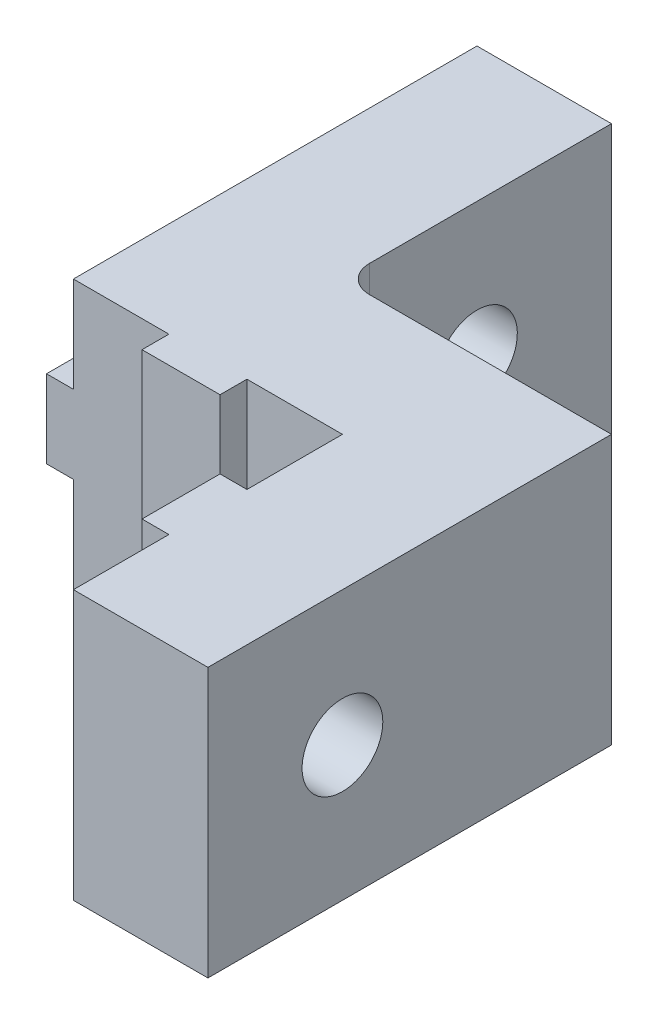
SolidWorks part; units mm, degrees
ref_plane "Front Plane" through (0, 0, 0) normal (0, 0, 1) x (1, 0, 0)
ref_plane "Top Plane" through (0, 0, 0) normal (0, 1, 0) x (1, 0, 0)
ref_plane "Right Plane" through (0, 0, 0) normal (1, 0, 0) x (0, 0, -1)
sketch "Sketch1" plane through (0, 0, 0) normal (0, 0, 1) x (1, 0, 0)
  line L0 (0, 10) -> (0, 6.45)
  line L1 (0, 6.45) -> (-1, 6.45)
  line L2 (-1, 6.45) -> (-1, 3.55)
  line L3 (-1, 3.55) -> (0, 3.55)
  line L4 (0, 3.55) -> (0, 0)
  line L5 (0, 0) -> (15, 0)
  line L6 (15, 0) -> (15, 10)
  line L7 (15, 10) -> (0, 10)
  dimension "D1" = 1
  dimension "D2" = 10
  dimension "D3" = 2.9
  dimension "D4" = 15
extrude "Main" add sketch "Sketch1" along normal blind 25
sketch "Sketch2" plane through (0, 0, 0) normal (0, -1, 0) x (-1, 0, 0)
  line L0 (0, -25) -> (0, 0) construction
  line L1 (1, -15) -> (1, -25)
  line L2 (-15, 0) -> (-5, 0)
  line L3 (1, -25) -> (-10, -25)
  line L4 (-15, 0) -> (-15, -10)
  line L5 (-15, -10) -> (-5, -10)
  line L6 (1, -25) -> (1, 0) construction
  line L7 (-5, 0) -> (-5, -10)
  line L8 (-10, -25) -> (-10, -21.45)
  line L9 (0, -25) -> (0, 0) construction
  line L10 (0, -25) -> (-15, -25) construction
  line L11 (-10, -21.45) -> (-9, -21.45)
  line L12 (-9, -21.45) -> (-9, -18.55)
  line L13 (-9, -18.55) -> (-10, -18.55)
  line L14 (-10, -18.55) -> (-10, -15)
  line L15 (-10, -15) -> (-6.45, -15)
  line L16 (-6.45, -15) -> (-6.45, -16)
  line L17 (-6.45, -16) -> (-3.55, -16)
  line L18 (-3.55, -16) -> (-3.55, -15)
  line L19 (-3.55, -15) -> (1, -15)
  dimension "D1" = 10
  dimension "D2" = 5
  dimension "D3" = 10
  dimension "D4" = 1
  dimension "D5" = 2.9
  dimension "D6" = 10
  dimension "D7" = 3.55
  dimension "D8" = 3.55
  dimension "D9" = 2.9
extrude "VerticalForm" cut sketch "Sketch2" against normal through all
sketch "Sketch3" plane through (15, 0, 0) normal (1, 0, 0) x (0, 0, -1)
  line L0 (0, 10) -> (0, 0) construction
  line L1 (-10, 10) -> (0, 10) construction
  line L2 (-25, 0) -> (-25, 10) construction
  circle A0 centre (-5, 5) radius 1.5
  circle A1 centre (-20, 5) radius 1.5
  dimension "D1" = 3
  dimension "D2" = 5
  dimension "D3" = 5
  dimension "D4" = 5
extrude "MakerBeamFixHole" cut sketch "Sketch3" against normal through all
fillet "Fillet1" radius 1 1 edges at (5, 5, 10)
